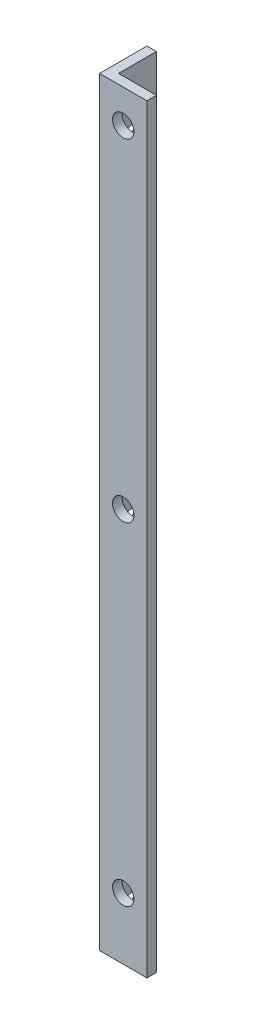
SolidWorks part; units mm, degrees
ref_plane "Спереди" through (0, 0, 0) normal (0, 0, 1) x (1, 0, 0)
ref_plane "Сверху" through (0, 0, 0) normal (0, 1, 0) x (1, 0, 0)
ref_plane "Справа" through (0, 0, 0) normal (1, 0, 0) x (0, 0, -1)
sketch "Эскиз1" plane through (0, 0, 0) normal (0, 1, 0) x (1, 0, 0)
  line L0 (0, 10) -> (0, 0)
  line L1 (0, 0) -> (10, 0)
  line L2 (10, 0) -> (10, 2)
  line L3 (10, 2) -> (2, 2)
  line L4 (2, 2) -> (2, 10)
  line L5 (2, 10) -> (0, 10)
  dimension "D1" = 2
  dimension "D2" = 2
  dimension "D3" = 10
  dimension "D4" = 10
extrude "Бобышка-Вытянуть1" add sketch "Эскиз1" along normal blind 160
sketch "Эскиз2" plane through (0, 0, 0) normal (0, 0, 1) x (1, 0, 0)
  line L0 (0, 0) -> (10, 0) construction
  line L1 (0, 160) -> (0, 0) construction
  circle A0 centre (5, 13) radius 2.25
  circle A1 centre (5, 83) radius 2.25
  circle A2 centre (5, 153) radius 2.25
  dimension "D1" = 70
  dimension "D2" = 70
  dimension "D3" = 13
  dimension "D4" = 4.5
  dimension "D5" = 5
extrude "Вырез-Вытянуть1" cut sketch "Эскиз2" against normal up to next
sketch "Эскиз3" plane through (0, 0, 0) normal (-1, 0, 0) x (0, 0, 1)
  line L0 (0, 160) -> (0, 0) construction
  line L1 (-10, 160) -> (0, 160) construction
  circle A0 centre (-5, 7) radius 2.25
  circle A1 centre (-5, 77) radius 2.25
  circle A2 centre (-5, 147) radius 2.25
  dimension "D1" = 4.5
  dimension "D2" = 5
  dimension "D3" = 70
  dimension "D4" = 70
  dimension "D5" = 13
extrude "Вырез-Вытянуть2" cut sketch "Эскиз3" against normal up to next
